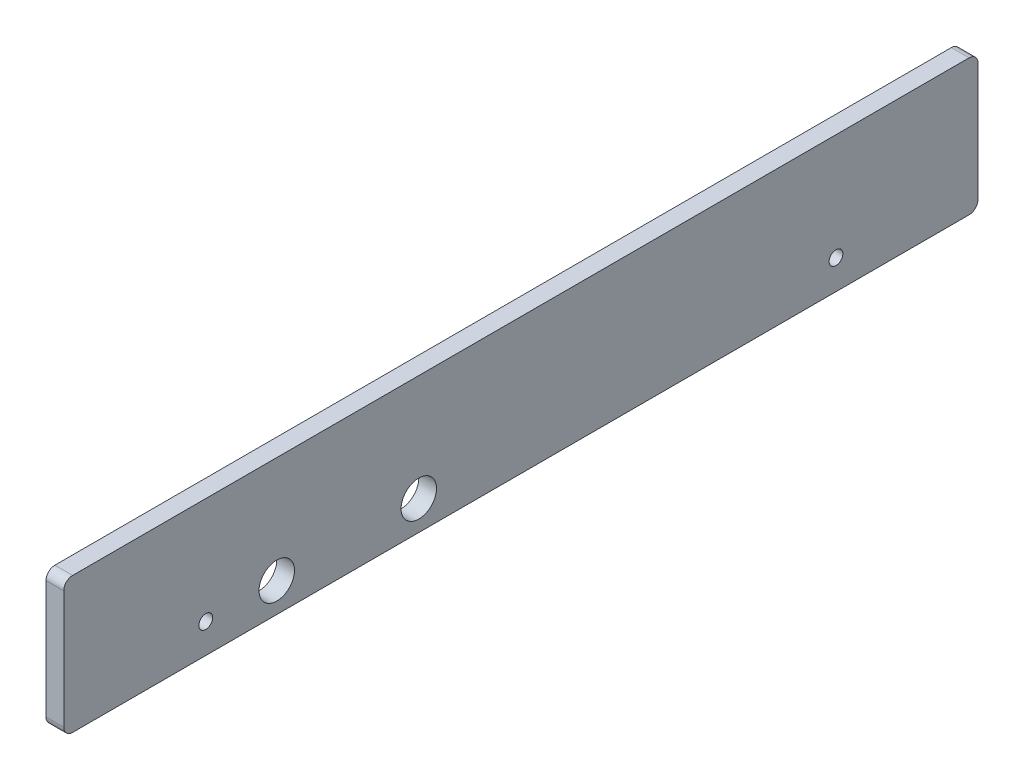
SolidWorks part; units mm, degrees
material "PE High Density"
ref_plane "Front Plane" through (0, 0, 0) normal (0, 0, 1) x (1, 0, 0)
ref_plane "Top Plane" through (0, 0, 0) normal (0, 1, 0) x (1, 0, 0)
ref_plane "Right Plane" through (0, 0, 0) normal (1, 0, 0) x (0, 0, -1)
sketch "Sketch1" plane through (0, 0, 0) normal (1, 0, 0) x (0, 0, -1)
  line L1 (0, 0) -> (327.025, 0)
  line L2 (0, 0) -> (0, 48.6359)
  line L3 (0, 48.6359) -> (327.025, 48.6359)
  line L4 (327.025, 0) -> (327.025, 48.6359)
  circle A0 centre (50.8, 10.5359) radius 2.4574
  circle A1 centre (276.225, 10.5359) radius 2.4575
  circle A2 centre (76.2, 10.5359) radius 6.35
  circle A3 centre (127, 10.5359) radius 6.35
  dimension "D3" = 4.9149
  dimension "D7" = 4.9149
  dimension "D10" = 12.7
  dimension "D1" = 48.6359
  dimension "D2" = 327.025
  dimension "D4" = 50.8
  dimension "D5" = 225.425
  dimension "D6" = 38.1
  dimension "D8" = 25.4
  dimension "D9" = 50.8
extrude "Boss-Extrude1" add sketch "Sketch1" along normal blind 6.35
fillet "Fillet1" radius 3.175 4 edges at (3.175, 48.6359, -327.025) (3.175, 0, -327.025) (3.175, 0, 0) (3.175, 48.6359, 0)
